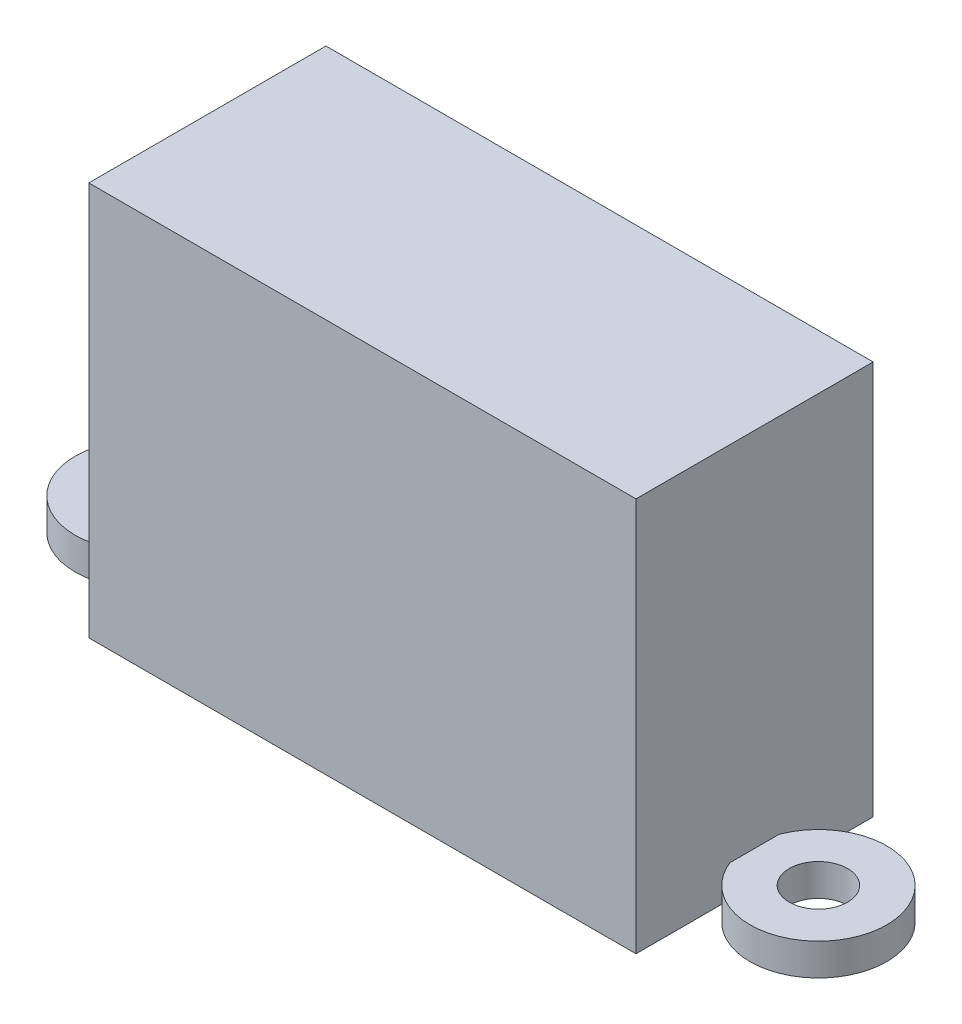
SolidWorks part; units mm, degrees
ref_plane "Front Plane" through (0, 0, 0) normal (0, 0, 1) x (1, 0, 0)
ref_plane "Top Plane" through (0, 0, 0) normal (0, 1, 0) x (1, 0, 0)
ref_plane "Right Plane" through (0, 0, 0) normal (1, 0, 0) x (0, 0, -1)
sketch "Sketch1" plane through (0, 0, 0) normal (0, 1, 0) x (1, 0, 0)
  line L0 (-18.5, 0) -> (18.5, 0) construction
  circle A0 centre (-18.5, 0) radius 1.6
  circle A1 centre (-18.5, 0) radius 3.75
  circle A2 centre (18.5, 0) radius 1.6
  circle A3 centre (18.5, 0) radius 3.75
  point P4 (0, 0)
  point P9 (0, 0)
  dimension "D2" = 3.2
  dimension "D3" = 7.5
  dimension "D1" = 37
extrude "Boss-Extrude1" add sketch "Sketch1" along normal blind 1.75
sketch "Sketch2" plane through (0, 0, 0) normal (0, 1, 0) x (1, 0, 0)
  line L1 (-15, 6.5) -> (15, 6.5)
  line L2 (-15, 6.5) -> (-15, -6.5)
  line L3 (-15, -6.5) -> (15, -6.5)
  line L4 (15, 6.5) -> (15, -6.5)
  line L5 (-15, 6.5) -> (15, -6.5) construction
  line L6 (-15, -6.5) -> (15, 6.5) construction
  point P0 (0, 0)
  dimension "D1" = 30
  dimension "D2" = 13
extrude "Boss-Extrude2" add sketch "Sketch2" along normal blind 21.6 separate body
